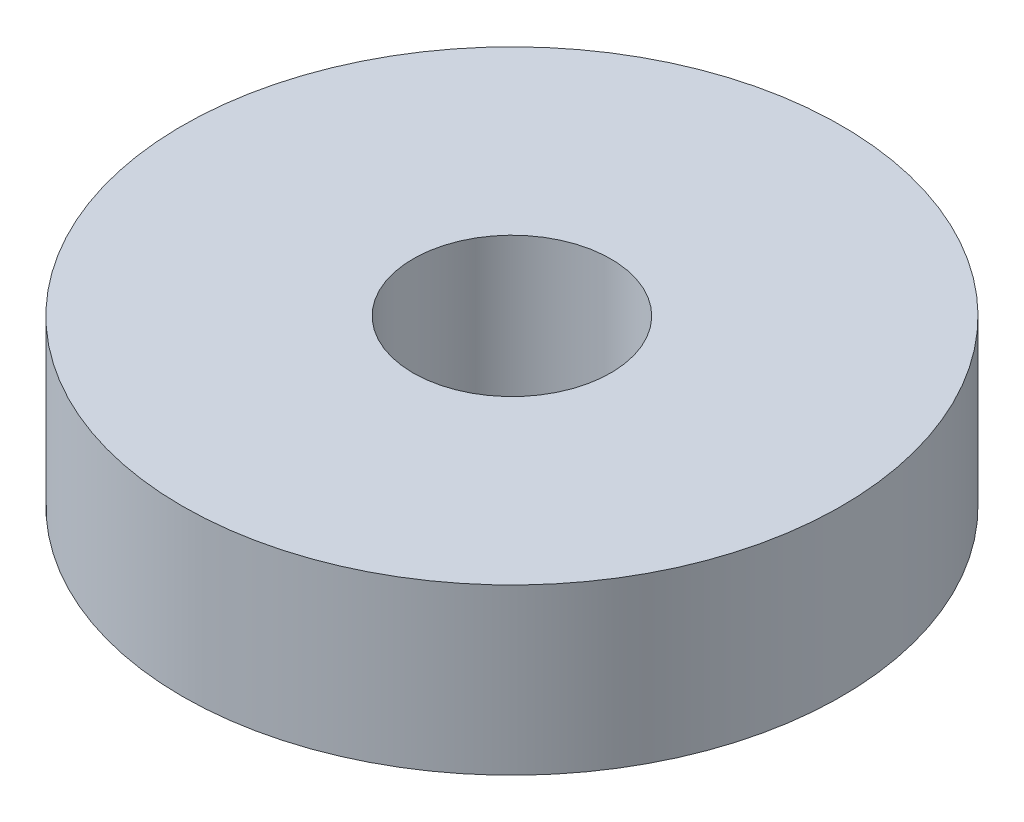
SolidWorks part; units mm, degrees
ref_plane "Front Plane" through (0, 0, 0) normal (0, 0, 1) x (1, 0, 0)
ref_plane "Top Plane" through (0, 0, 0) normal (0, 1, 0) x (1, 0, 0)
ref_plane "Right Plane" through (0, 0, 0) normal (1, 0, 0) x (0, 0, -1)
sketch "Sketch1" plane through (0, 0, 0) normal (0, 1, 0) x (1, 0, 0)
  circle A0 centre (0, 0) radius 6.35
  circle A1 centre (0, 0) radius 1.905
  dimension "D1" = 12.7
  dimension "D2" = 3.81
extrude "Boss-Extrude1" add sketch "Sketch1" along normal blind 3.175
